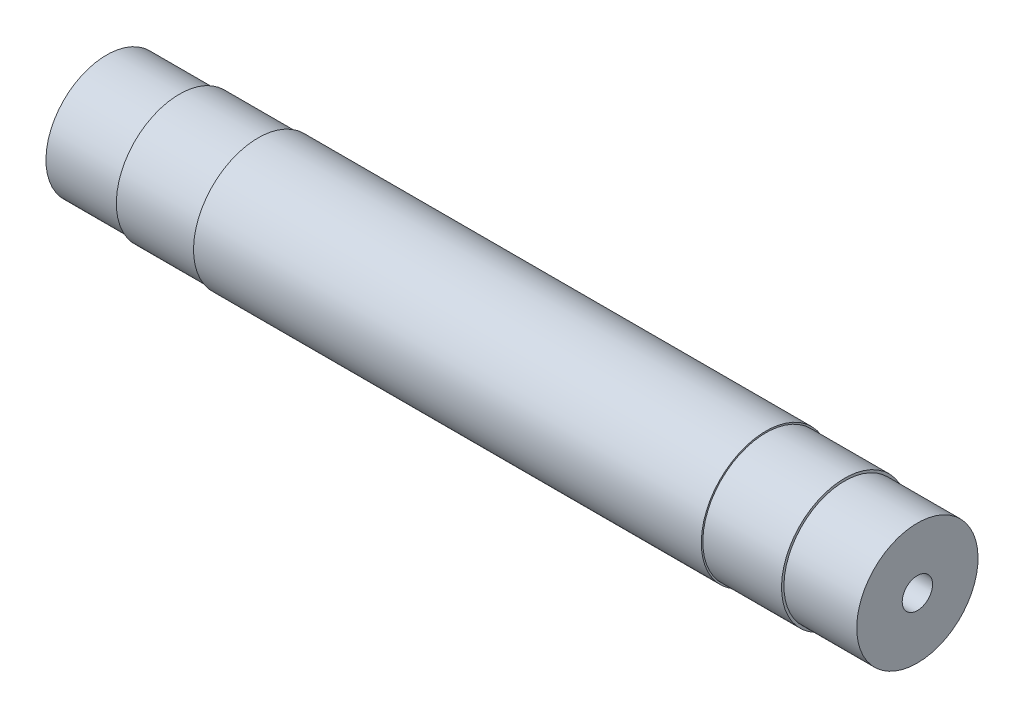
SolidWorks part; units mm, degrees
material "AISI 1020"
ref_plane "Спереди" through (0, 0, 0) normal (0, 0, 1) x (1, 0, 0)
ref_plane "Сверху" through (0, 0, 0) normal (0, 1, 0) x (1, 0, 0)
ref_plane "Справа" through (0, 0, 0) normal (1, 0, 0) x (0, 0, -1)
sketch "Эскиз1" plane through (0, 0, 0) normal (0, 0, 1) x (1, 0, 0)
  line L0 (0, 0) -> (0, 10.65) construction
  line L1 (-66.8416, 0) -> (-66.8416, 10) construction
  line L2 (-54.8416, 10) -> (-66.8416, 10) construction
  line L3 (-41.8614, 10.4) -> (-54.8416, 10.4) construction
  line L4 (0, 10.65) -> (-41.8614, 10.65) construction
  line L5 (0, 0) -> (0, 10.65)
  line L6 (-66.8416, 0) -> (-66.8416, 10)
  line L7 (-54.8416, 10) -> (-66.8416, 10)
  line L8 (-41.8614, 10.4) -> (-54.8416, 10.4)
  line L9 (0, 10.65) -> (-41.8614, 10.65)
  line L10 (-66.8416, 0) -> (0, 0)
  line L11 (-54.8416, 10.4) -> (-54.8416, 10)
  line L12 (-41.8614, 10.65) -> (-41.8614, 10.4)
revolve "Повернуть1" add sketch "Эскиз1" angle 360 about L10
hole_wizard "Отверстие обработанное метчиком M61" positions "Эскиз2" profile "Эскиз3" tap size "M6" standard "ISO"
sketch "Эскиз2" plane through (-66.8416, 0, 0) normal (-1, 0, 0) x (0, 0, 1)
  point P0 (0, 0)
sketch "Эскиз3" plane through (-66.8416, 0, 0) normal (0, 1, 0) x (0, 0, 1)
  line L0 (0, 0) -> (0, 28.5022)
  line L1 (0, 28.5022) -> (2.5, 27)
  line L2 (2.5, 27) -> (2.5, 0)
  line L5 (2.5, 0) -> (0, 0)
  line L10 (0, 28.5022) -> (-2.5, 27) construction
  line L11 (0, -6.35) -> (0, 107.95) construction
  dimension "Диаметр сверла" = 5
  dimension "Глубина сверла" = 27
  dimension "Угол заточки сверла" = 118
cosmetic thread "Отверстие резьбы1" parameters "D1"=22, "D2"=6
mirror "Зеркальное отражение1" about plane through (0, 0, 0) normal (-1, 0, 0) of bodies 105 103
